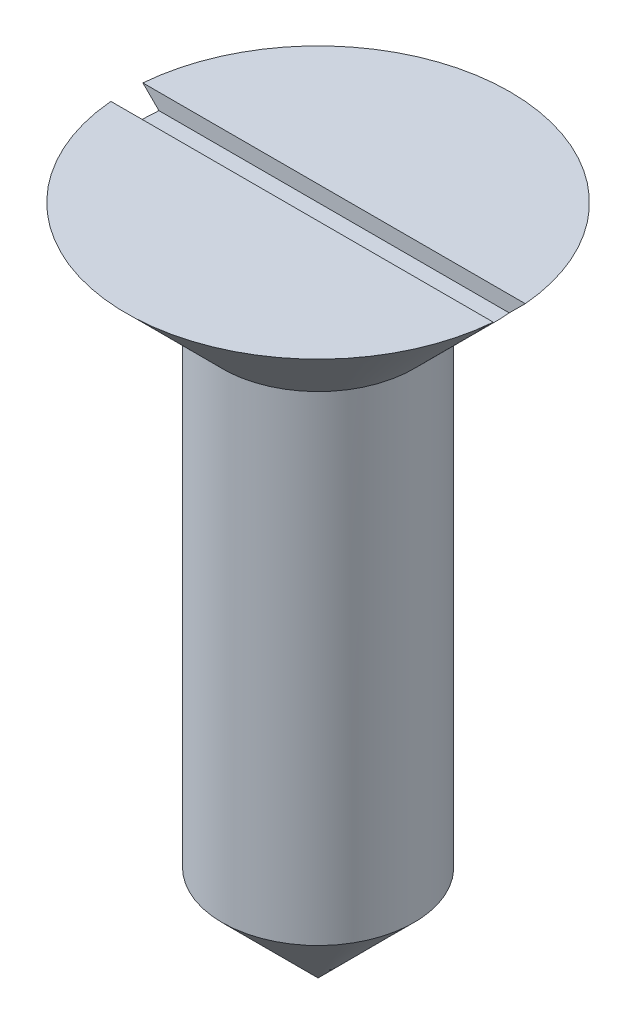
SolidWorks part; units mm, degrees
ref_plane "Front Plane" through (0, 0, 0) normal (0, 0, 1) x (1, 0, 0)
ref_plane "Top Plane" through (0, 0, 0) normal (0, 1, 0) x (1, 0, 0)
ref_plane "Right Plane" through (0, 0, 0) normal (1, 0, 0) x (0, 0, -1)
sketch "Sketch1" plane through (0, 0, 0) normal (0, 0, 1) x (1, 0, 0)
  line L0 (0, -39.28) -> (0, 34.8) construction
  line L1 (12, 12.4) -> (0, 12.4)
  line L2 (0, 6.48) -> (0, 12.4)
  line L4 (12, 12.4) -> (6, 6.4)
  line L5 (6, 6.4) -> (6, -23.6)
  line L6 (6, -23.6) -> (0, -29.6)
  line L7 (0, 6.48) -> (0, -29.6)
revolve "Revolve2" add sketch "Sketch1" angle 360 about L0
sketch "Sketch2" plane through (0, 0, 0) normal (1, 0, 0) x (0, 0, -1)
  line L0 (12, 12.4) -> (-12, 12.4) construction
  line L1 (1, 13.4) -> (-1, 13.4)
  line L2 (1, 13.4) -> (1, 11.4)
  line L3 (1, 11.4) -> (-1, 11.4)
  line L4 (-1, 13.4) -> (-1, 11.4)
  line L5 (1, 13.4) -> (-1, 11.4) construction
  line L6 (1, 11.4) -> (-1, 13.4) construction
  point P0 (0, 12.4)
  dimension "D1" = 2
  dimension "D2" = 2
extrude "Cut-Extrude1" cut sketch "Sketch2" against normal mid plane 100
